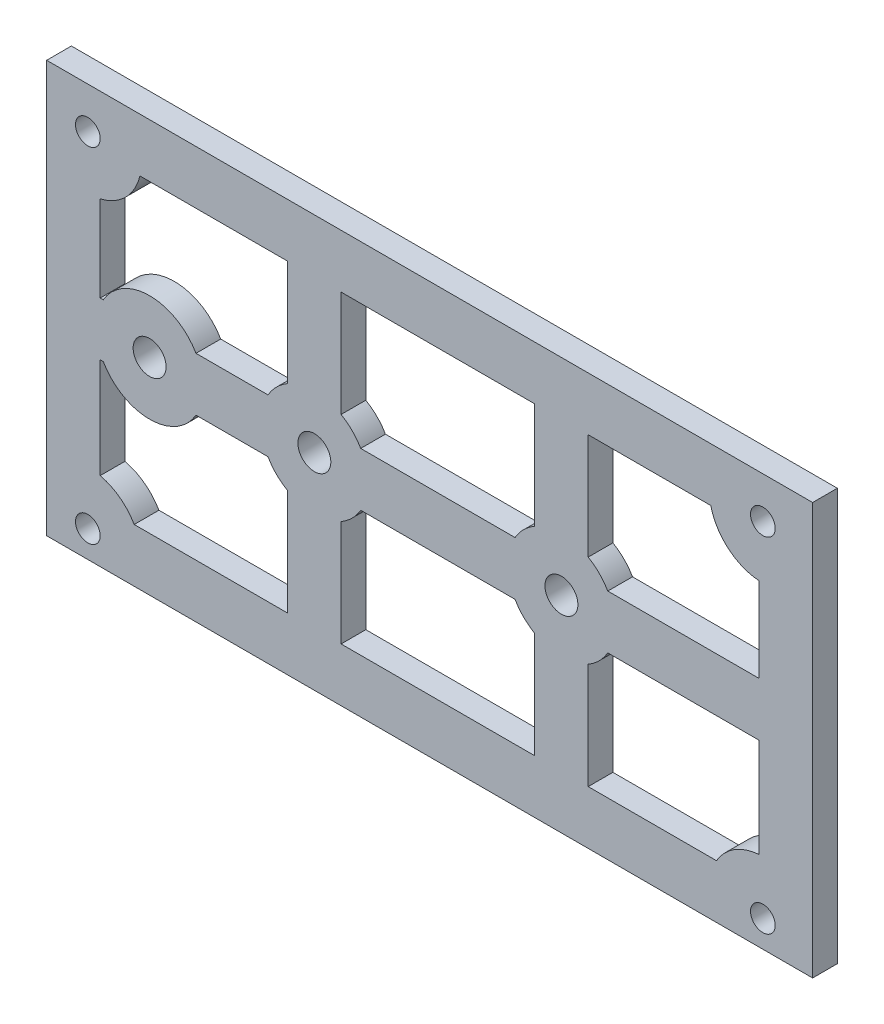
SolidWorks part; units mm, degrees
ref_plane "Front Plane" through (0, 0, 0) normal (0, 0, 1) x (1, 0, 0)
ref_plane "Top Plane" through (0, 0, 0) normal (0, 1, 0) x (1, 0, 0)
ref_plane "Right Plane" through (0, 0, 0) normal (1, 0, 0) x (0, 0, -1)
sketch "Sketch2" plane through (0, 0, 0) normal (0, 0, 1) x (1, 0, 0)
  line L1 (46.5, 25) -> (-46.5, 25)
  line L2 (46.5, 25) -> (46.5, -25)
  line L3 (46.5, -25) -> (-46.5, -25)
  line L4 (-46.5, 25) -> (-46.5, -25)
  line L5 (46.5, 25) -> (-46.5, -25) construction
  line L6 (46.5, -25) -> (-46.5, 25) construction
  point P0 (0, 0)
  dimension "D1" = 50
  dimension "D2" = 93
extrude "Boss-Extrude1" add sketch "Sketch2" along normal blind 3
sketch "Sketch1" plane through (0, 0, 0) normal (0, 0, 1) x (1, 0, 0)
  line L0 (18, 0) -> (14, 0) construction
  line L1 (-46.5, 25) -> (-45.6533, 25) construction
  line L2 (-46.5, 25) -> (-46.5, 24.1533) construction
  line L3 (-46.5, -25) -> (-35.8702, -25) construction
  line L4 (46.5, 25) -> (46.5, 22.3944) construction
  line L5 (-46.5, 25) -> (-45.9727, 24.7165) construction
  line L6 (-42.5136, -22.8568) -> (-40.0186, -21.5154) construction
  line L8 (-35.1754, 18.5) -> (-17.25, 18.5)
  line L9 (-40, 13.6754) -> (-40, 3.25)
  line L10 (-40, 3.25) -> (-39.6292, 3.25)
  line L11 (-17.25, 18.5) -> (-17.25, 5.6292)
  line L12 (-20.5, 0) -> (-27.5, 0) construction
  line L13 (-32, 0) -> (-36, 0) construction
  line L14 (16, 25) -> (16, 6.5) construction
  line L15 (19.25, 18.5) -> (34.1325, 18.5)
  line L16 (19.25, 18.5) -> (19.25, 5.6292)
  line L17 (21.6292, 3.25) -> (40, 3.25)
  line L18 (40, 13.5161) -> (40, 3.25)
  line L19 (45.2883, 24.3485) -> (46.5, 25) construction
  line L20 (-14, 25) -> (16, 25) construction
  line L21 (21.6292, -3.25) -> (40, -3.25)
  line L22 (19.25, -5.6292) -> (19.25, -18.5)
  line L23 (19.25, -18.5) -> (34.8286, -18.5)
  line L24 (40, -3.25) -> (40, -15.2672)
  line L25 (44.6104, 25) -> (46.5, 25) construction
  line L26 (-37.3467, 25) -> (-14, 25) construction
  line L27 (-10.75, 18.5) -> (12.75, 18.5)
  line L28 (-10.75, 18.5) -> (-10.75, 5.6292)
  line L29 (-8.3708, 3.25) -> (10.3708, 3.25)
  line L30 (12.75, 18.5) -> (12.75, 5.6292)
  line L31 (16, 25) -> (36.3038, 25) construction
  line L32 (34.41, 18.5) -> (45.2883, 24.3485) construction
  line L33 (-8.3708, -3.25) -> (10.3708, -3.25)
  line L34 (-10.75, -5.6292) -> (-10.75, -18.5)
  line L35 (-10.75, -18.5) -> (12.75, -18.5)
  line L36 (12.75, -5.6292) -> (12.75, -18.5)
  line L37 (46.5, 22.3944) -> (46.5, 17.6056) construction
  line L38 (46.5, -24.1455) -> (46.5, -25) construction
  line L39 (-40, -3.25) -> (-39.6292, -3.25)
  line L40 (-40, -3.25) -> (-40, -15.4266)
  line L41 (-35.8715, -18.5) -> (-17.25, -18.5)
  line L42 (-17.25, -5.6292) -> (-17.25, -18.5)
  line L43 (36.3038, 25) -> (44.6104, 25) construction
  line L44 (46.5, 17.6056) -> (46.5, 0) construction
  line L45 (-14, 25) -> (-14, 6.5) construction
  line L46 (46.5, 0) -> (22.5, 0) construction
  line L47 (46.5, 0) -> (46.5, -19.3567) construction
  line L48 (46.5, -19.3567) -> (46.5, -24.1455) construction
  line L49 (-35.0989, 18.8704) -> (-34.41, 18.5) construction
  line L50 (46.1821, -24.8291) -> (46.5, -25) construction
  line L51 (34.8273, -25) -> (46.0869, -25) construction
  line L52 (46.0869, -25) -> (46.5, -25) construction
  line L53 (16, -25) -> (34.8273, -25) construction
  line L54 (-14, -25) -> (16, -25) construction
  line L55 (-14, -7.5269) -> (-14, -25) construction
  line L56 (-35.8702, -25) -> (-14, -25) construction
  line L57 (-46.5, -25) -> (-42.5136, -22.8568) construction
  line L58 (-46.5, -17.5978) -> (-46.5, -25) construction
  line L59 (-46.5, 0) -> (-46.5, -17.5978) construction
  line L60 (-40.5, 0) -> (-46.5, 0) construction
  line L61 (-46.5, 15.8467) -> (-46.5, 0) construction
  line L62 (-46.5, 24.1533) -> (-46.5, 15.8467) construction
  line L63 (-45.9727, 24.7165) -> (-35.0989, 18.8704) construction
  line L64 (-34.41, 18.5) -> (34.41, -18.5) construction
  line L65 (-45.6533, 25) -> (-37.3467, 25) construction
  line L66 (19.25, 5.6292) -> (19.25, 3.25) construction
  line L67 (19.25, 3.25) -> (21.6292, 3.25) construction
  line L68 (10.3708, 3.25) -> (12.75, 3.25) construction
  line L69 (12.75, 5.6292) -> (12.75, 3.25) construction
  line L70 (19.25, -3.25) -> (21.6292, -3.25) construction
  line L71 (19.25, -3.25) -> (19.25, -5.6292) construction
  line L72 (10.3708, -3.25) -> (12.75, -3.25) construction
  line L73 (12.75, -3.25) -> (12.75, -5.6292) construction
  line L74 (-19.6292, 3.25) -> (-17.25, 3.25) construction
  line L75 (-17.25, 5.6292) -> (-17.25, 3.25) construction
  line L76 (-14, 6.5) -> (-14, 2) construction
  line L77 (-14, 2) -> (-14, -2) construction
  line L78 (-10.75, 5.6292) -> (-10.75, 3.25) construction
  line L79 (-10.75, 3.25) -> (-8.3708, 3.25) construction
  line L80 (-7.5, 0) -> (-12, 0) construction
  line L81 (-12, 0) -> (-20.5, 0) construction
  line L82 (16, 6.5) -> (16, 2) construction
  line L83 (16, 2) -> (16, -2) construction
  line L84 (22.5, 0) -> (18, 0) construction
  line L85 (16, -2) -> (16, -6.5) construction
  line L86 (16, -6.5) -> (16, -25) construction
  line L87 (14, 0) -> (9.5, 0) construction
  line L88 (9.5, 0) -> (-7.5, 0) construction
  line L89 (-36, 0) -> (-40.5, 0) construction
  line L90 (-39.6292, 3.25) -> (-28.3708, 3.25) construction
  line L91 (-28.3708, 3.25) -> (-19.6292, 3.25)
  line L92 (-27.5, 0) -> (-32, 0) construction
  line L93 (-39.6292, -3.25) -> (-28.3708, -3.25) construction
  line L94 (-28.3708, -3.25) -> (-19.6292, -3.25)
  line L95 (-19.6292, -3.25) -> (-17.25, -3.25) construction
  line L96 (-17.25, -3.25) -> (-17.25, -5.6292) construction
  line L97 (-14, -2) -> (-14, -6.5) construction
  line L98 (-14, -6.5) -> (-14, -7.5269) construction
  line L99 (-10.75, -3.25) -> (-10.75, -5.6292) construction
  line L100 (-10.75, -3.25) -> (-8.3708, -3.25) construction
  line L101 (-40.0186, -21.5154) -> (-35.5577, -19.117) construction
  line L102 (-35.5577, -19.117) -> (34.1652, 18.3684) construction
  line L103 (34.41, 18.5) -> (40, 18.5) construction
  line L104 (40, 18.5) -> (40, 13.5161) construction
  line L105 (-40, 18.5) -> (-40, 13.6754) construction
  line L106 (-40, 18.5) -> (-35.1754, 18.5) construction
  line L107 (-40, -15.4266) -> (-40, -18.5) construction
  line L108 (-40, -18.5) -> (-35.8715, -18.5) construction
  line L109 (40, -15.2672) -> (40, -18.5) construction
  line L110 (34.8286, -18.5) -> (40, -18.5) construction
  line L111 (34.1325, 18.5) -> (34.41, 18.5) construction
  line L112 (34.1652, 18.3684) -> (34.41, 18.5) construction
  line L113 (34.41, -18.5) -> (34.732, -18.6731) construction
  line L114 (34.732, -18.6731) -> (46.5, -25) construction
  circle A0 centre (-34, 0) radius 2
  circle A1 centre (-14, 0) radius 2
  circle A2 centre (16, 0) radius 2
  circle A3 centre (40.4571, 20) radius 1.5
  circle A4 centre (40.4571, -21.7511) radius 1.5
  circle A5 centre (-41.5, -21.7511) radius 1.5
  circle A6 centre (-41.5, 20) radius 1.5
  arc A8 (34.1325, 18.5) -> (40, 13.5161) centre (40.4571, 20) ccw
  arc A9 (-45.9727, 24.7165) -> (-46.5, 24.1533) centre (-41.5, 20) ccw construction
  arc A10 (-46.5, -17.5978) -> (-35.8702, -25) centre (-41.5, -21.7511) ccw construction
  arc A11 (40, -15.2672) -> (34.8286, -18.5) centre (40.4571, -21.7511) ccw
  arc A12 (-28.3708, 3.25) -> (-39.6292, 3.25) centre (-34, 0) ccw
  arc A13 (-8.3708, 3.25) -> (-10.75, 5.6292) centre (-14, 0) ccw
  arc A14 (21.6292, 3.25) -> (19.25, 5.6292) centre (16, 0) ccw
  arc A15 (22.5, 0) -> (21.6292, 3.25) centre (16, 0) ccw construction
  arc A16 (21.6292, -3.25) -> (22.5, 0) centre (16, 0) ccw construction
  arc A17 (16, -6.5) -> (19.25, -5.6292) centre (16, 0) ccw construction
  arc A18 (19.25, -5.6292) -> (21.6292, -3.25) centre (16, 0) ccw
  arc A19 (12.75, -5.6292) -> (16, -6.5) centre (16, 0) ccw construction
  arc A20 (9.5, 0) -> (10.3708, -3.25) centre (16, 0) ccw construction
  arc A21 (10.3708, -3.25) -> (12.75, -5.6292) centre (16, 0) ccw
  arc A22 (10.3708, 3.25) -> (9.5, 0) centre (16, 0) ccw construction
  arc A23 (16, 6.5) -> (12.75, 5.6292) centre (16, 0) ccw construction
  arc A24 (12.75, 5.6292) -> (10.3708, 3.25) centre (16, 0) ccw
  arc A25 (19.25, 5.6292) -> (16, 6.5) centre (16, 0) ccw construction
  arc A26 (-7.5, 0) -> (-8.3708, 3.25) centre (-14, 0) ccw construction
  arc A27 (-10.75, 5.6292) -> (-14, 6.5) centre (-14, 0) ccw construction
  arc A28 (-17.25, 5.6292) -> (-19.6292, 3.25) centre (-14, 0) ccw
  arc A29 (-14, 6.5) -> (-17.25, 5.6292) centre (-14, 0) ccw construction
  arc A30 (-8.3708, -3.25) -> (-7.5, 0) centre (-14, 0) ccw construction
  arc A31 (-14, -6.5) -> (-10.75, -5.6292) centre (-14, 0) ccw construction
  arc A32 (-10.75, -5.6292) -> (-8.3708, -3.25) centre (-14, 0) ccw
  arc A33 (-17.25, -5.6292) -> (-14, -6.5) centre (-14, 0) ccw construction
  arc A34 (-20.5, 0) -> (-19.6292, -3.25) centre (-14, 0) ccw construction
  arc A35 (-19.6292, -3.25) -> (-17.25, -5.6292) centre (-14, 0) ccw
  arc A36 (-19.6292, 3.25) -> (-20.5, 0) centre (-14, 0) ccw construction
  arc A37 (-28.3708, -3.25) -> (-27.5, 0) centre (-34, 0) ccw construction
  arc A38 (-27.5, 0) -> (-28.3708, 3.25) centre (-34, 0) ccw construction
  arc A39 (-39.6292, 3.25) -> (-40.5, 0) centre (-34, 0) ccw construction
  arc A40 (-39.6292, -3.25) -> (-28.3708, -3.25) centre (-34, 0) ccw
  arc A41 (-40.5, 0) -> (-39.6292, -3.25) centre (-34, 0) ccw construction
  arc A42 (-40, -15.4266) -> (-46.5, -17.5978) centre (-41.5, -21.7511) ccw construction
  arc A43 (-35.8702, -25) -> (-35.5577, -19.117) centre (-41.5, -21.7511) ccw construction
  arc A44 (-35.8715, -18.5) -> (-40, -15.4266) centre (-41.5, -21.7511) ccw
  arc A45 (-37.3467, 25) -> (-45.6533, 25) centre (-41.5, 20) ccw construction
  arc A46 (-35.0989, 18.8704) -> (-37.3467, 25) centre (-41.5, 20) ccw construction
  arc A47 (-46.5, 24.1533) -> (-46.5, 15.8467) centre (-41.5, 20) ccw construction
  arc A48 (-40, 13.6754) -> (-35.1754, 18.5) centre (-41.5, 20) ccw
  arc A49 (-46.5, 15.8467) -> (-40, 13.6754) centre (-41.5, 20) ccw construction
  arc A50 (44.6104, 25) -> (36.3038, 25) centre (40.4571, 20) ccw construction
  arc A51 (46.5, 17.6056) -> (46.5, 22.3944) centre (40.4571, 20) ccw construction
  arc A52 (45.2883, 24.3485) -> (44.6104, 25) centre (40.4571, 20) ccw construction
  arc A53 (46.5, 22.3944) -> (45.2883, 24.3485) centre (40.4571, 20) ccw construction
  arc A54 (40, 13.5161) -> (46.5, 17.6056) centre (40.4571, 20) ccw construction
  arc A55 (36.3038, 25) -> (34.1325, 18.5) centre (40.4571, 20) ccw construction
  arc A56 (46.5, -19.3567) -> (34.8286, -18.5) centre (40.4571, -21.7511) ccw construction
  arc A57 (46.5, -24.1455) -> (46.5, -19.3567) centre (40.4571, -21.7511) ccw construction
  arc A58 (34.8273, -25) -> (46.0869, -25) centre (40.4571, -21.7511) ccw construction
  arc A59 (46.0869, -25) -> (46.5, -24.1455) centre (40.4571, -21.7511) ccw
  arc A60 (34.732, -18.6731) -> (34.8273, -25) centre (40.4571, -21.7511) ccw construction
  arc A61 (-45.6533, 25) -> (-45.9727, 24.7165) centre (-41.5, 20) ccw construction
  arc A62 (-35.1754, 18.5) -> (-35.0989, 18.8704) centre (-41.5, 20) ccw construction
  arc A63 (34.8286, -18.5) -> (34.732, -18.6731) centre (40.4571, -21.7511) ccw construction
  arc A64 (34.8286, -18.5) -> (34.732, -18.6731) centre (40.4571, -21.7511) ccw construction
  arc A65 (-35.5577, -19.117) -> (-35.8715, -18.5) centre (-41.5, -21.7511) ccw construction
  point P0 (0, 0)
  point P6 (0, 0)
  dimension "D2" = 3
  dimension "D11" = 4
  dimension "D3" = 13
  dimension "D5" = 20
  dimension "D6" = 30
  dimension "D7" = 50
  dimension "D9" = 30.5
  dimension "D8" = 12.5
  dimension "D4" = 5
  dimension "D10" = 5
  dimension "D12" = 3.2489
  dimension "D13" = 6.5
  dimension "D14" = 6.5
  dimension "D15" = 6.5
  dimension "D16" = 6.5
  dimension "D17" = 6.5
  dimension "D18" = 6.5
  dimension "D19" = 6.5
extrude "Cut-Extrude9" cut sketch "Sketch1" along normal through all from surface at 0 contours A14 L17 L18 A8 L15 L16 | A24 L30 L27 L28 A13 L29 | A48 L9 L10 A12 L91 A28 L11 L8 | A44 L41 L42 A35 L94 A40 L39 L40 | A32 L34 L35 L36 A21 L33 | A18 L22 L23 A11 L24 L21 | A3 | A6 | A0 | A1 | A2 | A4 | A5 starting at face at (0, 0, 0)
equation "\"gearAxle\"= 4mm"
equation "\"boltDiameter\"=3"
equation "\"D2@Sketch1\"=\"boltDiameter\""
equation "\"addendum\"= \"addendumFactor\" / \"pitch\""
